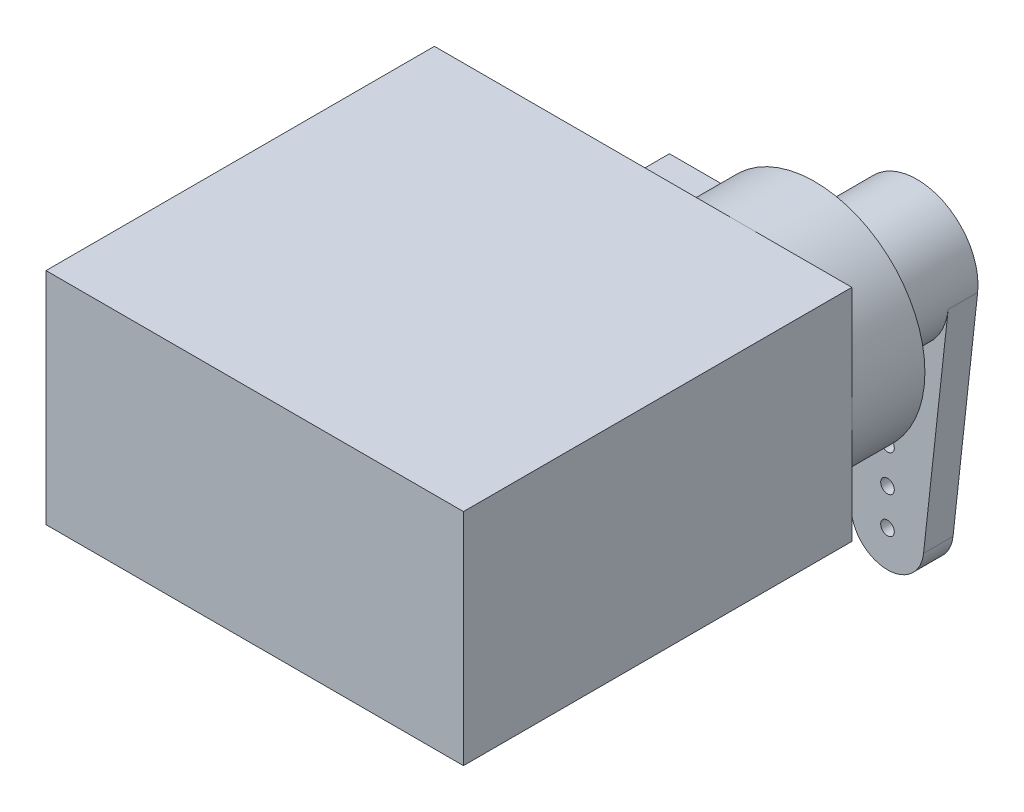
SolidWorks part; units mm, degrees
ref_plane "Front Plane" through (0, 0, 0) normal (0, 0, 1) x (1, 0, 0)
ref_plane "Top Plane" through (0, 0, 0) normal (0, 1, 0) x (1, 0, 0)
ref_plane "Right Plane" through (0, 0, 0) normal (1, 0, 0) x (0, 0, -1)
sketch "Sketch1" plane through (0, 0, 0) normal (0, 1, 0) x (1, 0, 0)
  line L1 (-11.684, 10.8712) -> (11.684, 10.8712)
  line L2 (-11.684, 10.8712) -> (-11.684, -10.8712)
  line L3 (-11.684, -10.8712) -> (11.684, -10.8712)
  line L4 (11.684, 10.8712) -> (11.684, -10.8712)
  line L5 (-11.684, 10.8712) -> (11.684, -10.8712) construction
  line L6 (-11.684, -10.8712) -> (11.684, 10.8712) construction
  point P0 (0, 0)
  dimension "D1" = 23.368
  dimension "D2" = 21.7424
extrude "Boss-Extrude1" add sketch "Sketch1" along normal blind 12.319
sketch "Sketch2" plane through (0, 0, -10.8712) normal (0, 0, -1) x (-1, 0, 0)
  line L0 (-11.684, 12.319) -> (11.684, 12.319) construction
  line L1 (-11.684, 12.319) -> (-11.684, 0) construction
  line L2 (-11.684, 0) -> (11.684, 0) construction
  line L3 (-5.5245, 6.1595) -> (10.7569, 6.1595) construction
  line L4 (-0.4163, 2.7178) -> (2.6162, 2.7178)
  line L6 (-0.4163, 9.6012) -> (2.6162, 9.6012)
  line L7 (2.6162, 2.7178) -> (2.6162, 9.6012)
  arc A0 (-0.4163, 9.6012) -> (-0.4163, 2.7178) centre (-5.5245, 6.1595) ccw
  point P10 (2.6162, 6.1595)
  dimension "D1" = 14.3002
  dimension "D2" = 6.8834
extrude "Boss-Extrude2" add sketch "Sketch2" along normal blind 4.0894
sketch "Sketch3" plane through (0, 0, -14.9606) normal (0, 0, -1) x (-1, 0, 0)
  circle A0 centre (-5.5245, 6.1595) radius 3.4163
  arc A1 (-0.4163, 9.6012) -> (-0.4163, 2.7178) centre (-5.5245, 6.1595) ccw construction
  dimension "D1" = 6.8326
extrude "Boss-Extrude3" add sketch "Sketch3" along normal blind 4.064
sketch "Sketch4" plane through (0, 0, -19.0246) normal (0, 0, -1) x (-1, 0, 0)
  line L0 (-8.9203, 5.786) -> (-7.5443, -6.7246)
  line L1 (-3.5047, -6.7246) -> (-2.1287, 5.786)
  circle A0 centre (-5.5245, 6.1595) radius 3.4163 construction
  circle A1 centre (-5.5245, 6.1595) radius 3.4163 construction
  arc A2 (-7.5443, -6.7246) -> (-3.5047, -6.7246) centre (-5.5245, -6.5024) ccw
  arc A3 (-2.1287, 5.786) -> (-8.9203, 5.786) centre (-5.5245, 6.1595) ccw
  point P12 (-5.5245, 9.5758)
  dimension "D1" = 2.032
  dimension "D2" = 16.0782
extrude "Boss-Extrude4" add sketch "Sketch4" along normal blind 1.651
sketch "Sketch5" plane through (0, 0, -20.6756) normal (0, 0, -1) x (-1, 0, 0)
  circle A0 centre (-5.5245, -6.5024) radius 0.381
  arc A2 (-7.5443, -6.7246) -> (-3.5047, -6.7246) centre (-5.5245, -6.5024) ccw construction
  circle A3 centre (-5.5245, -4.4704) radius 0.381
  circle A4 centre (-5.5245, -2.4384) radius 0.381
  circle A5 centre (-5.5245, -0.4064) radius 0.381
  circle A6 centre (-5.5245, 1.6256) radius 0.381
  dimension "D1" = 0.762
  dimension "D3" = 2.032
  dimension "D2" = 5
extrude "Cut-Extrude1" cut sketch "Sketch5" against normal up to surface (29.8435 mm away)
